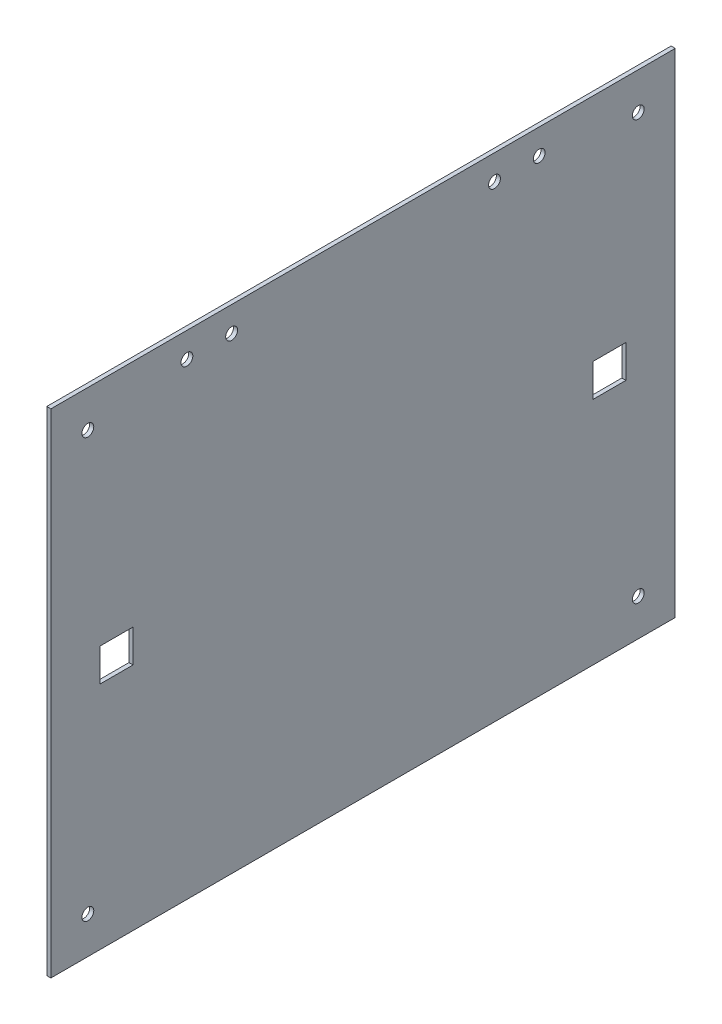
SolidWorks part; units mm, degrees
ref_plane "Front Plane" through (0, 0, 0) normal (0, 0, 1) x (1, 0, 0)
ref_plane "Top Plane" through (0, 0, 0) normal (0, 1, 0) x (1, 0, 0)
ref_plane "Right Plane" through (0, 0, 0) normal (1, 0, 0) x (0, 0, -1)
sketch "Sketch1" plane through (0, 0, 0) normal (1, 0, 0) x (0, 0, -1)
  line L1 (0, 0) -> (241.3, 0)
  line L2 (0, 0) -> (0, 190.5)
  line L3 (0, 190.5) -> (241.3, 190.5)
  line L4 (241.3, 0) -> (241.3, 190.5)
  dimension "D1" = 241.3
  dimension "D2" = 190.5
extrude "Boss-Extrude1" add sketch "Sketch1" along normal blind 1.5875
sketch "Sketch2" plane through (1.5875, 0, 0) normal (1, 0, 0) x (0, 0, -1)
  line L2 (-1000, 95.25) -> (49000, 95.25) construction
  line L3 (0, 190.5) -> (0, 0) construction
  line L4 (120.65, -809.5) -> (120.65, 49190.5) construction
  line L5 (241.3, 190.5) -> (0, 190.5) construction
  line L6 (1228.6, 95.25) -> (-48771.4, 95.25) construction
  line L7 (0, 0) -> (241.3, 0) construction
  line L8 (241.3, 0) -> (241.3, 190.5) construction
  circle A8 centre (227.0125, 14.2875) radius 2.286
  circle A9 centre (227.0125, 176.2125) radius 2.286
  circle A10 centre (14.2875, 14.2875) radius 2.286
  circle A11 centre (14.2875, 176.2125) radius 2.286
  point P15 (0, 95.25)
  point P20 (120.65, 190.5)
  dimension "D1" = 4.572
  dimension "D2" = 14.2875
  dimension "D3" = 14.2875
extrude "Cut-Extrude1" cut sketch "Sketch2" against normal through all
sketch "Sketch3" plane through (1.5875, 0, 0) normal (1, 0, 0) x (0, 0, -1)
  line L0 (54.864, 180.7845) -> (67.564, 180.7845) construction
  line L1 (173.736, 180.7845) -> (186.436, 180.7845) construction
  line L2 (241.3, 190.5) -> (0, 190.5) construction
  circle A0 centre (52.578, 180.7845) radius 2.286
  circle A1 centre (69.85, 180.7845) radius 2.286
  circle A2 centre (171.45, 180.7845) radius 2.286
  circle A3 centre (188.722, 180.7845) radius 2.286
  point P14 (120.65, 190.5)
  dimension "D2" = 4.572
  dimension "D1" = 12.7
  dimension "D3" = 12.7
  dimension "D4" = 9.7155
  dimension "D5" = 50.8
  dimension "D6" = 50.8
extrude "Cut-Extrude2" cut sketch "Sketch3" against normal through all
sketch "Sketch4" plane through (1.5875, 0, 0) normal (1, 0, 0) x (0, 0, -1)
  line L0 (0, 190.5) -> (0, 0) construction
  line L1 (19.05, 101.6) -> (31.75, 101.6)
  line L2 (19.05, 101.6) -> (19.05, 88.9)
  line L3 (19.05, 88.9) -> (31.75, 88.9)
  line L4 (31.75, 101.6) -> (31.75, 88.9)
  line L5 (209.55, 88.9) -> (222.25, 88.9)
  line L6 (209.55, 88.9) -> (209.55, 101.6)
  line L7 (209.55, 101.6) -> (222.25, 101.6)
  line L8 (222.25, 88.9) -> (222.25, 101.6)
  line L9 (241.3, 0) -> (241.3, 190.5) construction
  point P8 (19.05, 95.25)
  point P11 (0, 95.25)
  point P12 (209.55, 95.25)
  dimension "D1" = 12.7
  dimension "D2" = 12.7
  dimension "D3" = 19.05
  dimension "D4" = 19.05
extrude "Cut-Extrude3" cut sketch "Sketch4" against normal through all
